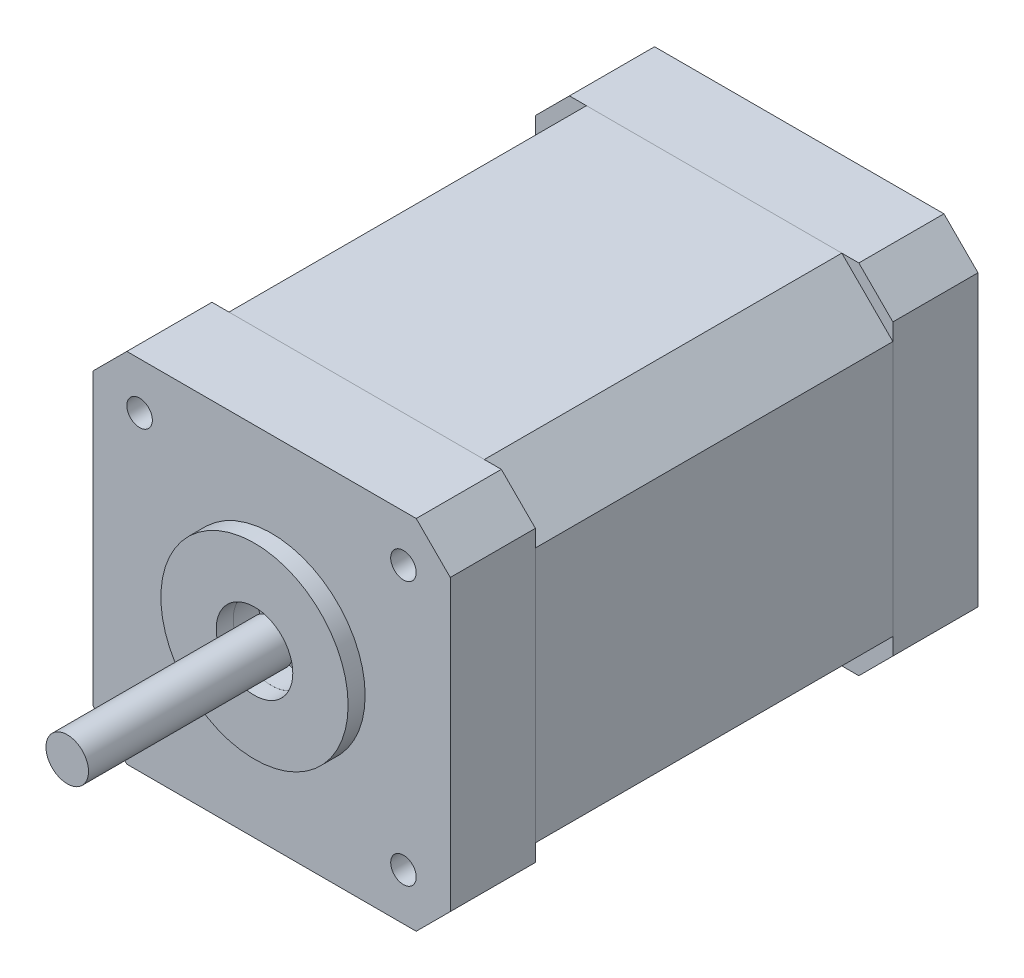
SolidWorks part; units mm, degrees
material "AISI 304"
ref_plane "前基準面" through (0, 0, 0) normal (0, 0, 1) x (1, 0, 0)
ref_plane "上基準面" through (0, 0, 0) normal (0, 1, 0) x (1, 0, 0)
ref_plane "右基準面" through (0, 0, 0) normal (1, 0, 0) x (0, 0, -1)
sketch "草圖1" plane through (0, 0, 0) normal (0, 0, 1) x (1, 0, 0)
  line L1 (-21, -21) -> (21, -21)
  line L2 (-21, -21) -> (-21, 21)
  line L3 (-21, 21) -> (21, 21)
  line L4 (21, -21) -> (21, 21)
  line L5 (-21, -21) -> (21, 21) construction
  line L6 (-21, 21) -> (21, -21) construction
  point P0 (0, 0)
  dimension "D1" = 42
  dimension "D2" = 42
extrude "填料-伸長1" add sketch "草圖1" along normal mid plane 42
chamfer "導角1" distance 6 angle 45 4 edges at (21, -21, 0) (-21, -21, 0) (-21, 21, 0) (21, 21, 0)
sketch "草圖15" plane through (0, 0, 21) normal (0, 0, 1) x (1, 0, 0)
  line L0 (15, 21) -> (-15, 21) construction
  line L1 (-21, -21) -> (21, -21)
  line L2 (-21, -21) -> (-21, 21)
  line L3 (-21, 21) -> (21, 21)
  line L4 (21, -21) -> (21, 21)
  line L5 (-21, -21) -> (21, 21) construction
  line L6 (-21, 21) -> (21, -21) construction
  line L7 (21, -15) -> (21, 15) construction
  point P0 (0, 0)
extrude "填料-伸長11" add sketch "草圖15" along normal blind 10 separate body
sketch "草圖16" plane through (0, 0, -21) normal (0, 0, -1) x (-1, 0, 0)
  line L1 (-21, -21) -> (21, -21)
  line L2 (-21, -21) -> (-21, 21)
  line L3 (-21, 21) -> (21, 21)
  line L4 (21, -21) -> (21, 21)
  line L5 (-21, -21) -> (21, 21) construction
  line L6 (-21, 21) -> (21, -21) construction
  line L8 (-15, 21) -> (15, 21) construction
  line L9 (21, 15) -> (21, -15) construction
  point P0 (0, 0)
extrude "填料-伸長12" add sketch "草圖16" along normal blind 10 separate body
chamfer "導角2" distance 4 angle 45 4 edges at (-21, -21, 26) (21, -21, 26) (21, 21, 26) (-21, 21, 26)
chamfer "導角3" distance 4 angle 45 4 edges at (-21, -21, -26) (21, -21, -26) (-21, 21, -26) (21, 21, -26)
sketch "草圖2" plane through (0, 0, 31) normal (0, 0, 1) x (1, 0, 0)
  circle A0 centre (0, 0) radius 11
  dimension "D1" = 22
extrude "填料-伸長2" add sketch "草圖2" along normal blind 2
sketch "草圖3" plane through (0, 0, 33) normal (0, 0, 1) x (1, 0, 0)
  circle A0 centre (0, 0) radius 4.5
  dimension "D1" = 9
extrude "除料-伸長1" cut sketch "草圖3" along direction (0, 0, -1) on the side against the normal blind 5
sketch "草圖6" plane through (0, 0, 31) normal (0, 0, 1) x (1, 0, 0)
  circle A0 centre (0, 0) radius 2.5
  dimension "D1" = 5
extrude "填料-伸長9" add sketch "草圖6" along direction (0, 0, 1) on the side of the normal offset from surface (24 mm away) 22 separate body
sketch "草圖8" plane through (0, 0, 31) normal (0, 0, 1) x (1, 0, 0)
  line L0 (0, 0) -> (0, 15.5) construction
  line L1 (0, 15.5) -> (-15.5, 15.5) construction
  circle A0 centre (-15.5, 15.5) radius 1.5
  dimension "D3" = 3
  dimension "D1" = 15.5
  dimension "D2" = 15.5
extrude "除料-伸長3" cut sketch "草圖8" against normal blind 4.5
sketch "草圖11" plane through (0, 0, 55) normal (0, 0, 1) x (1, 0, 0)
  line L0 (-2, 1.5) -> (2, 1.5)
  circle A0 centre (0, 0) radius 2.5 construction
  arc A1 (2, 1.5) -> (-2, 1.5) centre (0, 0) ccw
  point P5 (0, 1.5)
  point P6 (0, 2.5)
  dimension "D1" = 1
extrude "除料-伸長4" [suppressed] cut sketch "草圖11" against normal blind 18
pattern_circular "環狀複製排列1" count 4 over 360 about axis through (0, 0, 0) along (0, 0, 1) of "除料-伸長3"
